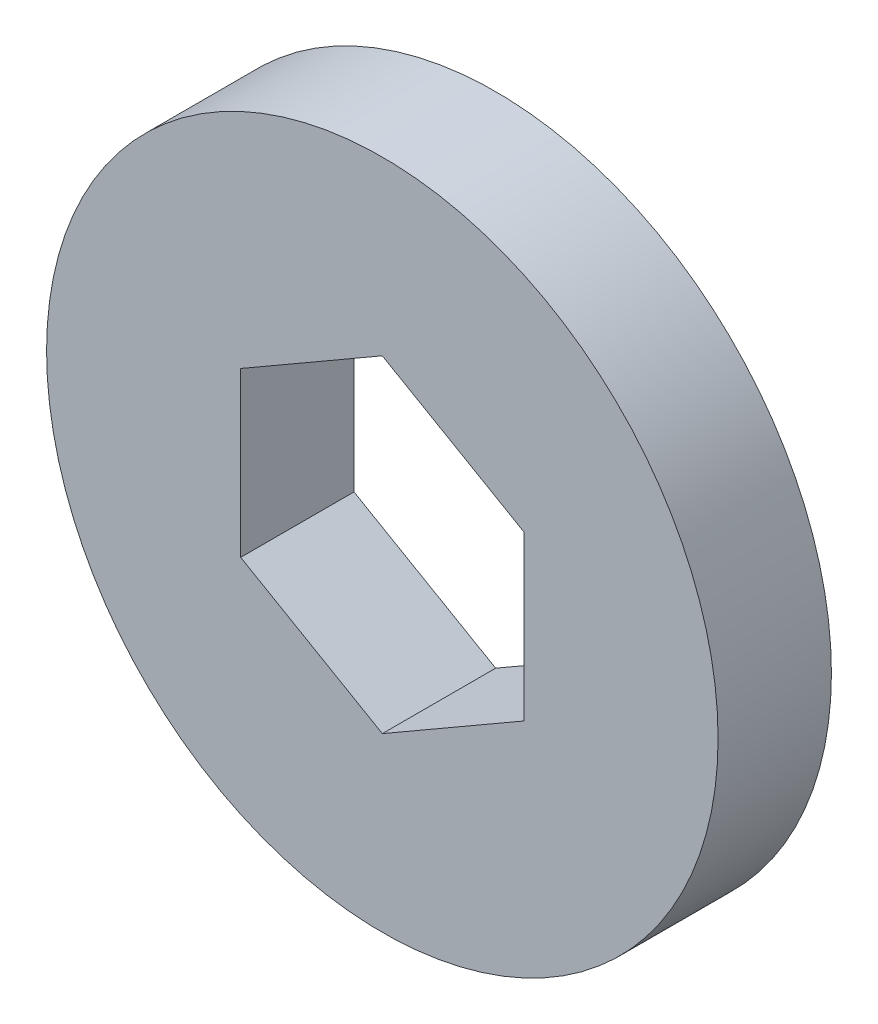
SolidWorks part; units mm, degrees
ref_plane "Front Plane" through (0, 0, 0) normal (0, 0, 1) x (1, 0, 0)
ref_plane "Top Plane" through (0, 0, 0) normal (0, 1, 0) x (1, 0, 0)
ref_plane "Right Plane" through (0, 0, 0) normal (1, 0, 0) x (0, 0, -1)
sketch "Sketch1" plane through (0, 0, 0) normal (0, 0, 1) x (1, 0, 0)
  circle A0 centre (0, 0) radius 11.85
  dimension "D1" = 23.7
extrude "Boss-Extrude1" add sketch "Sketch1" along normal blind 4
sketch "Sketch2" plane through (0, 0, 0) normal (0, 0, -1) x (-1, 0, 0)
  line L1 (0, 5.7735) -> (-5, 2.8868)
  line L2 (-5, 2.8868) -> (-5, -2.8868)
  line L3 (-5, -2.8868) -> (0, -5.7735)
  line L4 (0, -5.7735) -> (5, -2.8868)
  line L5 (5, -2.8868) -> (5, 2.8868)
  line L6 (5, 2.8868) -> (0, 5.7735)
  circle A0 centre (0, 0) radius 5 construction
  dimension "D1" = 10
extrude "Cut-Extrude1" cut sketch "Sketch2" against normal through all
